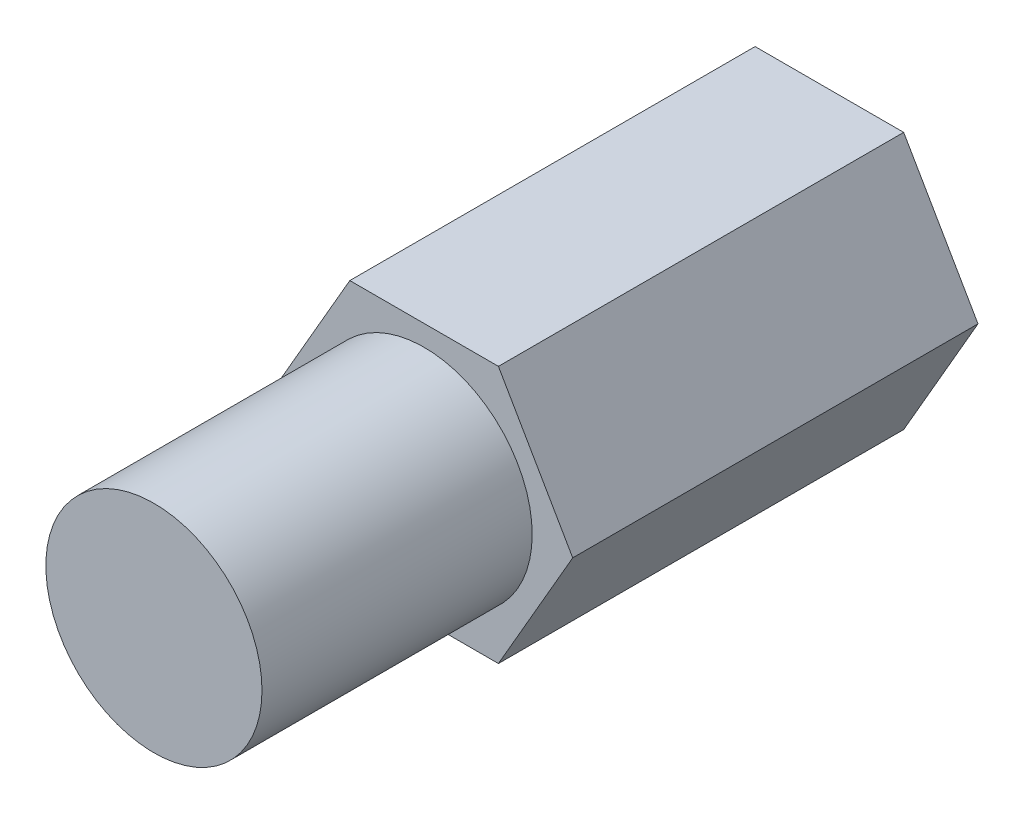
SolidWorks part; units mm, degrees
material "Brass"
ref_plane "Front" through (0, 0, 0) normal (0, 0, 1) x (1, 0, 0)
ref_plane "Top" through (0, 0, 0) normal (0, 1, 0) x (1, 0, 0)
ref_plane "Right" through (0, 0, 0) normal (1, 0, 0) x (0, 0, -1)
sketch "Sketch1" plane through (0, 0, 0) normal (0, 0, 1) x (1, 0, 0)
  line L1 (-5.5, 0) -> (-2.75, -4.7631)
  line L2 (-2.75, -4.7631) -> (2.75, -4.7631)
  line L3 (2.75, -4.7631) -> (5.5, 0)
  line L4 (5.5, 0) -> (2.75, 4.7631)
  line L5 (2.75, 4.7631) -> (-2.75, 4.7631)
  line L6 (-2.75, 4.7631) -> (-5.5, 0)
  circle A0 centre (0, 0) radius 4.7631 construction
  dimension "D1" = 11
extrude "Boss-Extrude1" add sketch "Sketch1" along normal blind 15
sketch "Sketch2" plane through (0, 0, 15) normal (0, 0, 1) x (1, 0, 0)
  circle A0 centre (0, 0) radius 4
  dimension "D1" = 8
extrude "Boss-Extrude2" add sketch "Sketch2" along normal blind 10
cosmetic thread "Cosmetic Thread1" parameters "D1"=8, "D2"=6.891
